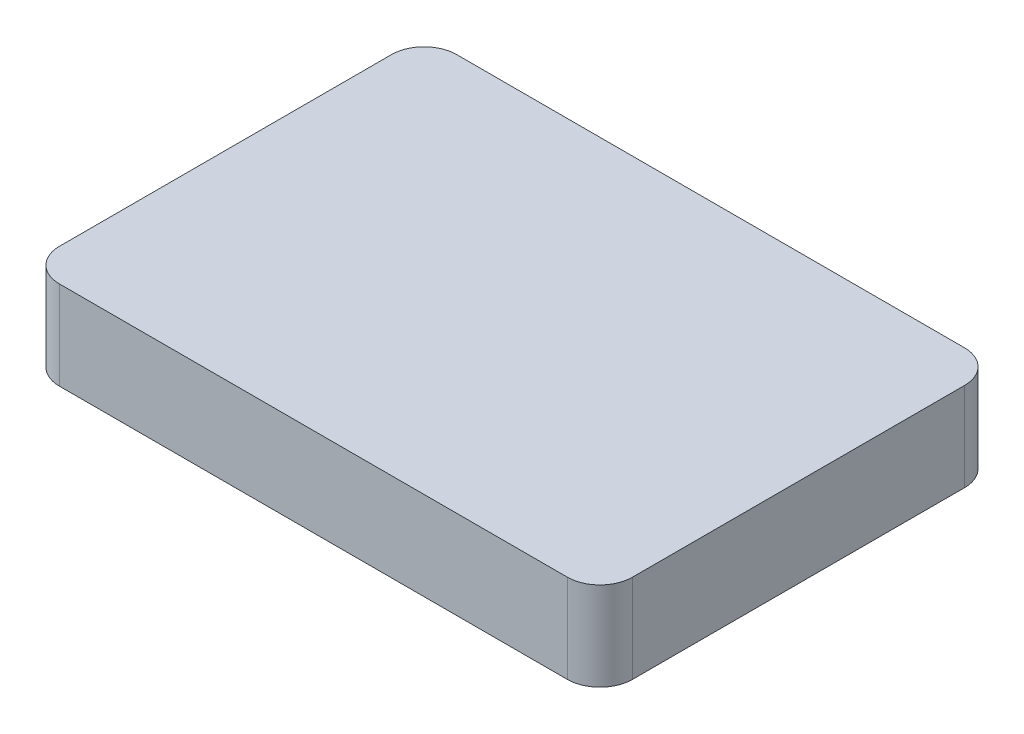
SolidWorks part; units mm, degrees
ref_plane "Front Plane" through (0, 0, 0) normal (0, 0, 1) x (1, 0, 0)
ref_plane "Top Plane" through (0, 0, 0) normal (0, 1, 0) x (1, 0, 0)
ref_plane "Right Plane" through (0, 0, 0) normal (1, 0, 0) x (0, 0, -1)
sketch "Sketch1" plane through (0, 0, 0) normal (0, 1, 0) x (1, 0, 0)
  line L1 (-22, -15.25) -> (22, -15.25)
  line L2 (-22, -15.25) -> (-22, 15.25)
  line L3 (-22, 15.25) -> (22, 15.25)
  line L4 (22, -15.25) -> (22, 15.25)
  line L5 (-22, -15.25) -> (22, 15.25) construction
  line L6 (-22, 15.25) -> (22, -15.25) construction
  point P0 (0, 0)
  dimension "D1" = 44
  dimension "D2" = 30.5
extrude "Boss-Extrude1" add sketch "Sketch1" along normal mid plane 6.8
fillet "Fillet1" radius 2.5 4 edges at (-22, 0, -15.25) (22, 0, -15.25) (22, 0, 15.25) (-22, 0, 15.25)
